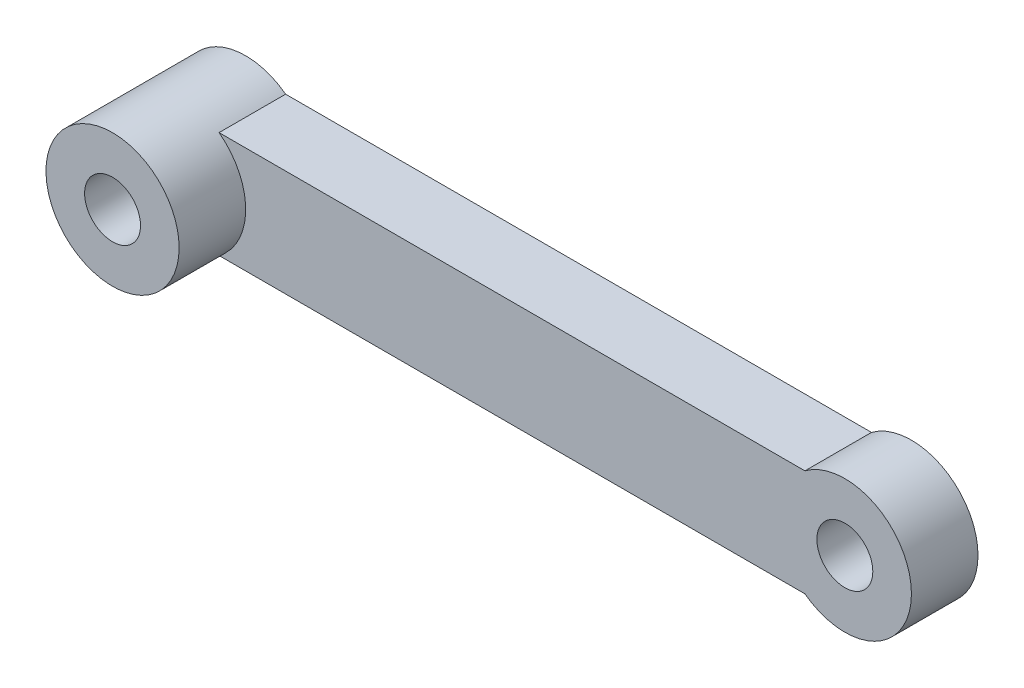
SolidWorks part; units mm, degrees
ref_plane "Front Plane" through (0, 0, 0) normal (0, 0, 1) x (1, 0, 0)
ref_plane "Top Plane" through (0, 0, 0) normal (0, 1, 0) x (1, 0, 0)
ref_plane "Right Plane" through (0, 0, 0) normal (1, 0, 0) x (0, 0, -1)
sketch "Sketch2" plane through (0, 0, 0) normal (0, 0, 1) x (1, 0, 0)
  line L0 (-40.0217, -5.7639) -> (-40.0217, 2.2361)
  line L1 (3.9783, -5.7639) -> (3.9783, 2.2361)
  line L2 (-40.0217, 2.2361) -> (3.9783, 2.2361)
  line L3 (-40.0217, -5.7639) -> (3.9783, -5.7639)
  circle A0 centre (-43.0217, -1.7639) radius 5
  circle A1 centre (6.9783, -1.7639) radius 5
  circle A2 centre (6.9783, -1.7639) radius 2.1
  circle A3 centre (-43.0217, -1.7639) radius 2.1
  dimension "D1" = 10
  dimension "D2" = 10
  dimension "D5" = 4.2
  dimension "D6" = 4.2
  dimension "D3" = 3
  dimension "D4" = 3
  dimension "D7" = 50
extrude "Boss-Extrude1" add sketch "Sketch2" along normal blind 5 contours L0 A0 A3 | L0 A0 | A1 L2 A0 L3 | L1 A1 A2 | L1 A1
sketch "Sketch3" plane through (0, 0, 5) normal (0, 0, 1) x (1, 0, 0)
  circle A0 centre (-43.0217, -1.7639) radius 2.1
  circle A1 centre (-43.0217, -1.7639) radius 5
  dimension "D1" = 10
  dimension "D2" = 4.2
extrude "Boss-Extrude2" add sketch "Sketch3" along normal blind 5
